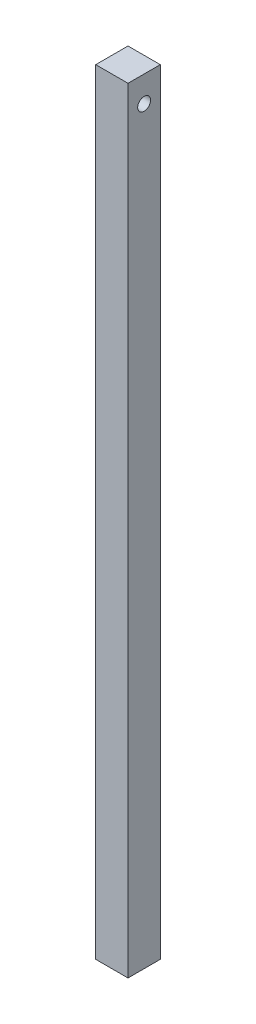
SolidWorks part; units mm, degrees
ref_plane "Front Plane" through (0, 0, 0) normal (0, 0, 1) x (1, 0, 0)
ref_plane "Top Plane" through (0, 0, 0) normal (0, 1, 0) x (1, 0, 0)
ref_plane "Right Plane" through (0, 0, 0) normal (1, 0, 0) x (0, 0, -1)
sketch "Sketch1" plane through (0, 0, 0) normal (0, 1, 0) x (1, 0, 0)
  line L1 (12.5, -12.5) -> (-12.5, -12.5)
  line L2 (12.5, -12.5) -> (12.5, 12.5)
  line L3 (12.5, 12.5) -> (-12.5, 12.5)
  line L4 (-12.5, -12.5) -> (-12.5, 12.5)
  line L5 (12.5, -12.5) -> (-12.5, 12.5) construction
  line L6 (12.5, 12.5) -> (-12.5, -12.5) construction
  point P0 (0, 0)
extrude "Boss-Extrude1" add sketch "Sketch1" along normal blind 500 and the other way blind 100
sketch "Sketch2" plane through (-12.5, 0, 0) normal (-1, 0, 0) x (0, 0, 1)
  circle A0 centre (0, 480) radius 5
extrude "Cut-Extrude1" cut sketch "Sketch2" against normal blind 500
